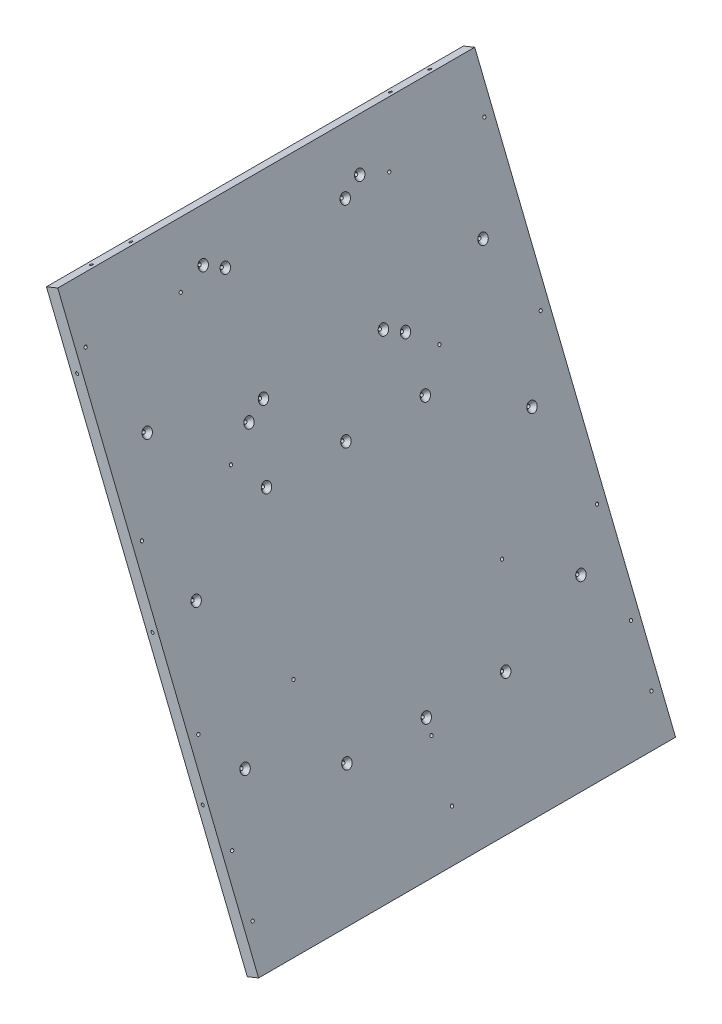
SolidWorks part; units mm, degrees
material "Beech"
ref_plane "Front Plane" through (0, 0, 0) normal (0, 0, 1) x (1, 0, 0)
ref_plane "Top Plane" through (0, 0, 0) normal (0, 1, 0) x (1, 0, 0)
ref_plane "Right Plane" through (0, 0, 0) normal (1, 0, 0) x (0, 0, -1)
sketch "Sketch1" plane through (0, 0, 0) normal (0, 0, 1) x (1, 0, 0)
  line L0 (274.6799, -487.2917) -> (65.3497, 30.8187)
  line L2 (274.6799, -487.2917) -> (262.9046, -492.0492)
  line L3 (262.9046, -492.0492) -> (53.5745, 26.0612)
  line L4 (65.3497, 30.8187) -> (53.5745, 26.0612)
  dimension "D2" = 12.7
  dimension "D3" = 558.8
extrude "Boss-Extrude1" add sketch "Sketch1" against normal up to surface (217.3 mm away) and the other way up to surface (217.3 mm away)
hole_wizard "Hole1" positions "Sketch2" profile "Sketch3" legacy
sketch "Sketch2" plane through (361.5328, -736.1625, 0) normal (-0.9272, -0.3746, 0) x (0, 0, 1)
  line L4 (-207.775, 822.0847) -> (-207.775, 404.0189) construction
  line L8 (-207.775, 822.0847) -> (-207.775, 717.5683)
  line L9 (-207.775, 717.5683) -> (-207.775, 613.0518)
  line L10 (-207.775, 613.0518) -> (-207.775, 508.5353)
  line L11 (-207.775, 508.5353) -> (-207.775, 404.0189)
  line L12 (-108.65, 822.0847) -> (-108.65, 404.0189) construction
  line L15 (0, 822.0847) -> (0, 613.0518) construction
  line L18 (-207.775, 390.7499) -> (-207.775, 276.5537) construction
  line L22 (-207.775, 390.7499) -> (-207.775, 362.2009)
  line L23 (-207.775, 362.2009) -> (-207.775, 333.6518)
  line L24 (-207.775, 333.6518) -> (-207.775, 305.1027)
  line L25 (-207.775, 305.1027) -> (-207.775, 276.5537)
  line L26 (0, 390.7499) -> (0, 276.5537) construction
  line L30 (0, 276.5537) -> (0, 305.1027)
  line L31 (0, 305.1027) -> (0, 333.6518)
  line L32 (0, 333.6518) -> (0, 362.2009)
  line L33 (0, 362.2009) -> (0, 390.7499)
  point P24 (-207.775, 613.0518)
  point P31 (-207.775, 456.2771)
  point P33 (-207.775, 769.8265)
  point P52 (-108.65, 456.2771)
  point P54 (-108.65, 630.1265)
  point P56 (-108.65, 769.8265)
  point P76 (-207.775, 362.2009)
  point P80 (-207.775, 305.1027)
  point P99 (0, 305.1027)
  point P104 (0, 362.2009)
  point P113 (207.775, 305.1027)
  point P114 (207.775, 362.2009)
  point P115 (108.65, 769.8265)
  point P116 (108.65, 630.1265)
  point P117 (108.65, 456.2771)
  point P118 (207.775, 769.8265)
  point P119 (207.775, 456.2771)
  point P120 (207.775, 613.0518)
  dimension "D1" = 139.7
sketch "Sketch3" plane through (131.8796, -167.7508, 207.775) normal (0, 0, 1) x (0.3746, -0.9272, 0)
  line L0 (0, 0) -> (0, 32.7039)
  line L1 (0, 32.7039) -> (1.5875, 31.75)
  line L2 (1.5875, 31.75) -> (1.5875, 4.0177)
  line L3 (1.5875, 4.0177) -> (5.08, 0)
  line L4 (5.08, 0) -> (0, 0)
  line L5 (0, -14.3089) -> (0, 102.4216) construction
  line L6 (0, 32.7039) -> (-1.5875, 31.75) construction
  line L7 (-1.5875, 4.0177) -> (-5.08, 0) construction
  dimension "Diameter" = 3.175
  dimension "Depth" = 31.75
  dimension "C-Sink Diameter" = 10.16
  dimension "C-Sink Angle" = 82
  dimension "Drill Angle" = 118
hole_wizard "Hole2" positions "Sketch4" profile "Sketch5" legacy
sketch "Sketch4" plane through (723.4984, -589.919, -230) normal (0, 0, -1) x (-1, 0, 0)
  line L0 (54.6742, 260.7254) -> (44.8416, 151.8686) construction
  line L6 (458.2175, 188.8136) -> (426.7882, 117.3689) construction
  line L11 (443.4217, 288.0956) -> (513.4071, 262.4897) construction
  line L16 (479.186, 443.3317) -> (498.5551, 428.1819) construction
  line L19 (643.2075, 626.7743) -> (602.3132, 525.5573) construction
  line L24 (664.0363, 618.3589) -> (454.7061, 100.2486) construction
  line L28 (664.0363, 618.3589) -> (611.7037, 488.8313)
  line L29 (611.7037, 488.8313) -> (559.3712, 359.3037)
  line L30 (559.3712, 359.3037) -> (507.0387, 229.7761)
  line L31 (507.0387, 229.7761) -> (454.7061, 100.2486)
  point P12 (52.9605, 241.7526)
  point P14 (47.6978, 183.4898)
  point P29 (434.4591, 134.8062)
  point P31 (453.1036, 177.1887)
  point P48 (478.4144, 275.2927)
  point P60 (488.8705, 435.7568)
  point P79 (636.0712, 609.1114)
  point P81 (609.4494, 543.2202)
  point P98 (559.3712, 359.3037)
  point P100 (507.0387, 229.7761)
  point P112 (637.87, 553.5951)
sketch "Sketch5" plane through (85.6283, -36.3239, -230) normal (1, 0, 0) x (0, 1, 0)
  line L0 (0, 0) -> (0, 32.7039)
  line L1 (0, 32.7039) -> (1.5875, 31.75)
  line L2 (1.5875, 31.75) -> (1.5875, 4.0177)
  line L3 (1.5875, 4.0177) -> (5.08, 0)
  line L4 (5.08, 0) -> (0, 0)
  line L5 (0, -14.3089) -> (0, 102.4216) construction
  line L6 (0, 32.7039) -> (-1.5875, 31.75) construction
  line L7 (-1.5875, 4.0177) -> (-5.08, 0) construction
  dimension "Diameter" = 3.175
  dimension "Depth" = 31.75
  dimension "C-Sink Diameter" = 10.16
  dimension "C-Sink Angle" = 82
  dimension "Drill Angle" = 118
hole_wizard "Hole3" positions "Sketch6" profile "Sketch7" legacy
sketch "Sketch6" plane through (723.4984, -589.919, 230) normal (0, 0, 1) x (1, 0, 0)
  point P4 (-507.0387, 229.7761)
  point P6 (-559.3712, 359.3037)
  point P8 (-637.87, 553.5951)
  point P10 (-636.0712, 609.1114)
  point P12 (-609.4494, 543.2202)
  point P14 (-488.8705, 435.7568)
  point P16 (-478.4144, 275.2927)
  point P18 (-453.1036, 177.1887)
  point P20 (-434.4591, 134.8062)
  point P22 (-52.9605, 241.7526)
  point P24 (-47.6978, 183.4898)
sketch "Sketch7" plane through (216.4597, -360.1428, 230) normal (1, 0, 0) x (0, -1, 0)
  line L0 (0, 0) -> (0, 32.7039)
  line L1 (0, 32.7039) -> (1.5875, 31.75)
  line L2 (1.5875, 31.75) -> (1.5875, 4.0177)
  line L3 (1.5875, 4.0177) -> (5.08, 0)
  line L4 (5.08, 0) -> (0, 0)
  line L5 (0, -14.3089) -> (0, 102.4216) construction
  line L6 (0, 32.7039) -> (-1.5875, 31.75) construction
  line L7 (-1.5875, 4.0177) -> (-5.08, 0) construction
  dimension "Diameter" = 3.175
  dimension "Depth" = 31.75
  dimension "C-Sink Diameter" = 10.16
  dimension "C-Sink Angle" = 82
  dimension "Drill Angle" = 118
hole_wizard "Hole4" positions "Sketch8" profile "Sketch9" legacy
sketch "Sketch8" plane through (373.3081, -731.405, 0) normal (0.9272, 0.3746, 0) x (0, 0, -1)
  point P49 (175, 685.961)
  point P51 (175, 549.8373)
  point P53 (175, 413.7135)
  point P67 (81.55, 779.6497)
  point P73 (81.55, 652.3446)
  point P79 (62.5, 662.9534)
  point P83 (62.5, 769.041)
  point P103 (-62.5, 769.041)
  point P105 (-62.5, 662.9534)
  point P106 (-81.55, 652.3446)
  point P109 (-81.55, 779.6497)
  point P110 (-175, 413.7135)
  point P111 (-175, 549.8373)
  point P112 (-175, 685.961)
  point P115 (-82.7375, 600.3846)
  point P117 (0, 600.3846)
  point P119 (82.7375, 600.3846)
  point P129 (0, 376.7378)
  point P131 (-82.7375, 376.7378)
  point P133 (82.7375, 376.7378)
sketch "Sketch9" plane through (116.3425, -95.3931, -175) normal (0, 0, 1) x (-0.3746, 0.9272, 0)
  line L0 (0, 0) -> (0, 32.7039)
  line L1 (0, 32.7039) -> (1.5875, 31.75)
  line L2 (1.5875, 31.75) -> (1.5875, 4.0177)
  line L3 (1.5875, 4.0177) -> (5.08, 0)
  line L4 (5.08, 0) -> (0, 0)
  line L5 (0, -14.3089) -> (0, 102.4216) construction
  line L6 (0, 32.7039) -> (-1.5875, 31.75) construction
  line L7 (-1.5875, 4.0177) -> (-5.08, 0) construction
  dimension "Diameter" = 3.175
  dimension "Depth" = 31.75
  dimension "C-Sink Diameter" = 10.16
  dimension "C-Sink Angle" = 82
  dimension "Drill Angle" = 118
hole_wizard "Hole5" positions "Sketch10" profile "Sketch11" legacy
sketch "Sketch10" plane through (410.7825, 184.08, 0) normal (-0.3746, 0.9272, 0) x (0, 0, -1)
  line L0 (207.775, 377.6924) -> (207.775, 288.0915) construction
  line L4 (108.65, 377.6924) -> (108.65, 288.0915) construction
  line L8 (175, 506.2803) -> (175, 390.3924) construction
  line L12 (94.25, 390.3924) -> (94.25, 377.6924) construction
  line L17 (94.25, 384.0424) -> (217.3, 384.0424) construction
  line L19 (94.25, 384.0424) -> (135.2667, 384.0424)
  line L20 (135.2667, 384.0424) -> (176.2833, 384.0424)
  line L21 (176.2833, 384.0424) -> (217.3, 384.0424)
  line L22 (0, 288.0915) -> (0, 390.3924) construction
  point P39 (108.65, 332.8919)
  point P41 (207.775, 332.8919)
  point P43 (175, 448.3363)
  point P47 (135.2667, 384.0424)
  point P49 (176.2833, 384.0424)
  point P65 (-175, 448.3363)
  point P66 (-135.2667, 384.0424)
  point P67 (-176.2833, 384.0424)
  point P68 (-207.775, 332.8919)
  point P69 (-108.65, 332.8919)
sketch "Sketch11" plane through (102.1305, 59.3765, 108.65) normal (0, 0, 1) x (-0.9272, -0.3746, 0)
  line L0 (0, 0) -> (0, 39.0539)
  line L1 (0, 39.0539) -> (1.5875, 38.1)
  line L2 (1.5875, 38.1) -> (1.5875, 4.0177)
  line L3 (1.5875, 4.0177) -> (5.08, 0)
  line L4 (5.08, 0) -> (0, 0)
  line L5 (0, -14.3089) -> (0, 102.4216) construction
  line L6 (0, 39.0539) -> (-1.5875, 38.1) construction
  line L7 (-1.5875, 4.0177) -> (-5.08, 0) construction
  dimension "Diameter" = 3.175
  dimension "Depth" = 38.1
  dimension "C-Sink Diameter" = 10.16
  dimension "C-Sink Angle" = 82
  dimension "Drill Angle" = 118
